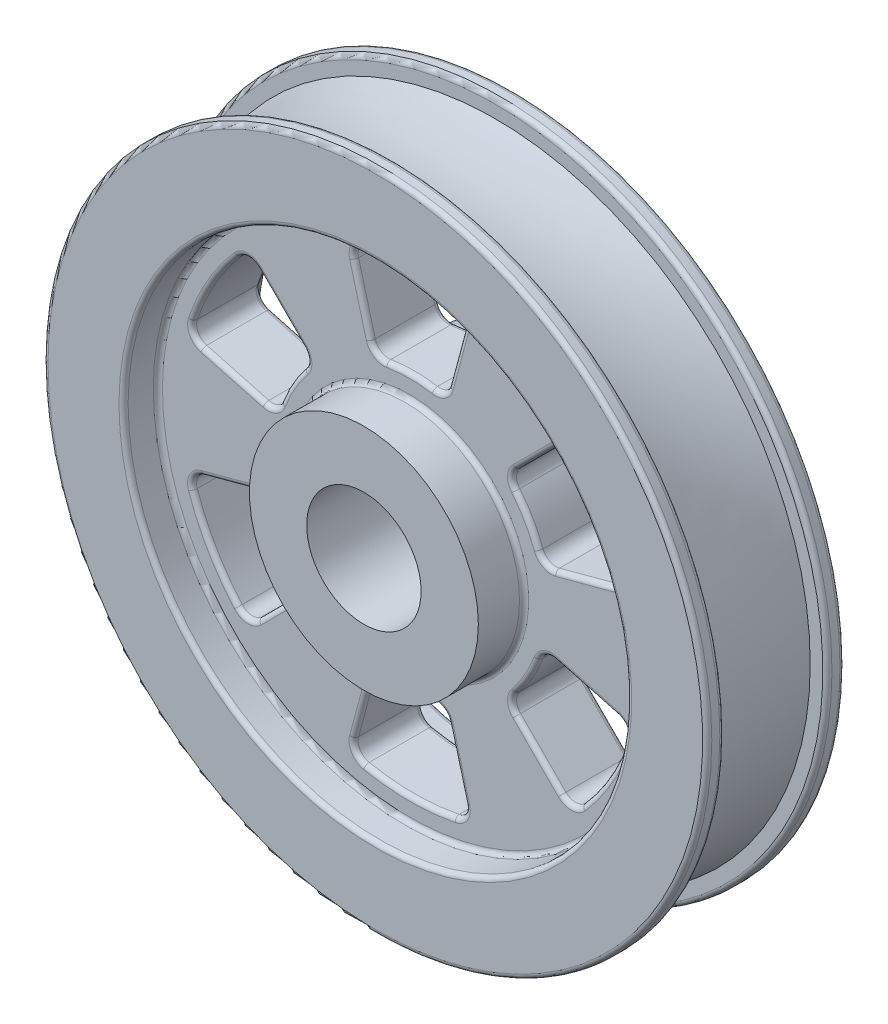
SolidWorks part; units mm, degrees
material "Cast Alloy Steel"
ref_plane "Front Plane" through (0, 0, 0) normal (0, 0, 1) x (1, 0, 0)
ref_plane "Top Plane" through (0, 0, 0) normal (0, 1, 0) x (1, 0, 0)
ref_plane "Right Plane" through (0, 0, 0) normal (1, 0, 0) x (0, 0, -1)
sketch "Wheel Cross-section" plane through (0, 0, 0) normal (1, 0, 0) x (0, 0, -1)
  line L0 (-130.7747, 0) -> (134.6553, 0) construction
  line L1 (44.45, 31.75) -> (44.45, 63.5)
  line L2 (44.45, 63.5) -> (19.05, 63.5)
  line L3 (19.05, 63.5) -> (19.05, 139.7)
  line L4 (19.05, 139.7) -> (38.1, 139.7)
  line L5 (38.1, 139.7) -> (38.1, 184.15)
  line L6 (38.1, 184.15) -> (28.575, 184.15)
  line L7 (28.575, 184.15) -> (28.575, 174.625)
  line L9 (-28.575, 174.625) -> (-28.575, 184.15)
  line L10 (-28.575, 184.15) -> (-38.1, 184.15)
  line L11 (-38.1, 184.15) -> (-38.1, 139.7)
  line L12 (-38.1, 139.7) -> (-19.05, 139.7)
  line L13 (-19.05, 139.7) -> (-19.05, 63.5)
  line L14 (-19.05, 63.5) -> (-44.45, 63.5)
  line L15 (-44.45, 63.5) -> (-44.45, 31.75)
  line L17 (-44.45, 31.75) -> (44.45, 31.75)
  arc A0 (28.575, 174.625) -> (-28.575, 174.625) centre (0, 324.3221) cw
  dimension "D13" = 152.4
  dimension "D14" = 9.525
  dimension "D1" = 44.45
  dimension "D2" = 88.9
  dimension "D3" = 25.4
  dimension "D4" = 38.1
  dimension "D5" = 63.5
  dimension "D6" = 76.2
  dimension "D7" = 9.525
  dimension "D8" = 9.525
  dimension "D9" = 31.75
  dimension "D10" = 6.35
  dimension "D11" = 139.7
  dimension "D12" = 184.15
revolve "Revolve1" add sketch "Wheel Cross-section" angle 360 about L0
sketch "Spoke cut-out" plane through (0, 0, 19.05) normal (0, 0, 1) x (1, 0, 0)
  line L0 (0, 0) -> (-60.1063, 224.3199) construction
  line L1 (0, 0) -> (0, 216.2459) construction
  line L2 (0, 0) -> (59.3665, 221.5588) construction
  line L3 (30.8348, 115.0771) -> (21.6044, 80.6286)
  line L4 (-30.8348, 115.0771) -> (-21.6044, 80.6286)
  circle A0 centre (0, 0) radius 127 construction
  circle A1 centre (0, 0) radius 76.2 construction
  arc A2 (24.9728, 124.5205) -> (-24.9728, 124.5205) centre (0, 0) ccw
  arc A3 (12.9491, 75.0917) -> (-12.9491, 75.0917) centre (0, 0) ccw
  arc A4 (24.9728, 124.5205) -> (30.8348, 115.0771) centre (23.4745, 117.0493) cw
  arc A5 (-24.9728, 124.5205) -> (-30.8348, 115.0771) centre (-23.4745, 117.0493) ccw
  arc A6 (-12.9491, 75.0917) -> (-21.6044, 80.6286) centre (-14.244, 82.6008) cw
  arc A7 (12.9491, 75.0917) -> (21.6044, 80.6286) centre (14.244, 82.6008) ccw
  point P13 (32.87, 122.6726)
  point P16 (-32.87, 122.6726)
  point P19 (-19.722, 73.6035)
  point P22 (19.722, 73.6035)
  dimension "D1" = 254
  dimension "D2" = 152.4
  dimension "D5" = 7.62
  dimension "D6" = 7.62
  dimension "D7" = 7.62
  dimension "D3" = 15
  dimension "D4" = 15
extrude "Spoke hole" cut sketch "Spoke cut-out" against normal through all
pattern_circular "Spoke hole pattern" count 6 over 360 about axis through (0, 0, 0) along (0, 0, 1) of "Spoke hole"
fillet "0.10 inch Fillets & Rounds" radius 2.54 106 edges at (-89.8737, -86.4702, -19.05) (-109.9852, -63.5, -19.05) (-119.8223, -34.5978, -19.05) (-97.8529, -26.2196, -19.05) (-75.1507, -22.1991, -19.05) (-65.9911, -38.1, -19.05) (-56.8003, -53.9828, -19.05) (-18.3504, -76.1819, -19.05) (0, -76.2, -19.05) (18.3504, -76.1819, -19.05) (26.2196, -97.8529, -19.05) (29.9485, -121.0681, -19.05) (0, -127, -19.05) (-29.9485, -121.0681, -19.05) (119.8223, -34.5978, -19.05) (109.9852, -63.5, -19.05) (89.8737, -86.4702, -19.05) (71.6333, -71.6333, -19.05) (56.8003, -53.9828, -19.05) (65.9911, -38.1, -19.05) (75.1507, -22.1991, -19.05) (89.8737, 86.4702, -19.05) (109.9852, 63.5, -19.05) (119.8223, 34.5978, -19.05) (97.8529, 26.2196, -19.05) (75.1507, 22.1991, -19.05) (65.9911, 38.1, -19.05) (56.8003, 53.9828, -19.05) (-29.9485, 121.0681, -19.05) (0, 127, -19.05) (29.9485, 121.0681, -19.05) (26.2196, 97.8529, -19.05) (18.3504, 76.1819, -19.05) (0, 76.2, -19.05) (-18.3504, 76.1819, -19.05) (-119.8223, 34.5978, -19.05) (-109.9852, 63.5, -19.05) (-89.8737, 86.4702, -19.05) (-71.6333, 71.6333, -19.05) (-56.8003, 53.9828, -19.05) (-65.9911, 38.1, -19.05) (-75.1507, 22.1991, -19.05) (18.3504, 76.1819, 19.05) (0, 76.2, 19.05) (-18.3504, 76.1819, 19.05) (-26.2196, 97.8529, 19.05) (-29.9485, 121.0681, 19.05) (0, 127, 19.05) (29.9485, 121.0681, 19.05) (75.1507, 22.1991, 19.05) (65.9911, 38.1, 19.05) (56.8003, 53.9828, 19.05) (71.6333, 71.6333, 19.05) (89.8737, 86.4702, 19.05) (109.9852, 63.5, 19.05) (119.8223, 34.5978, 19.05) (56.8003, -53.9828, 19.05) (65.9911, -38.1, 19.05) (75.1507, -22.1991, 19.05) (97.8529, -26.2196, 19.05) (119.8223, -34.5978, 19.05) (109.9852, -63.5, 19.05) (89.8737, -86.4702, 19.05) (-18.3504, -76.1819, 19.05) (0, -76.2, 19.05) (18.3504, -76.1819, 19.05) (26.2196, -97.8529, 19.05) (29.9485, -121.0681, 19.05) (0, -127, 19.05) (-29.9485, -121.0681, 19.05) (-119.8223, -34.5978, 19.05) (-97.8529, -26.2196, 19.05) (-75.1507, -22.1991, 19.05) (-65.9911, -38.1, 19.05) (-56.8003, -53.9828, 19.05) (-71.6333, -71.6333, 19.05) (-89.8737, -86.4702, 19.05) (-89.8737, 86.4702, 19.05) (-71.6333, 71.6333, 19.05) (-56.8003, 53.9828, 19.05) (-65.9911, 38.1, 19.05) (-75.1507, 22.1991, 19.05) (-97.8529, 26.2196, 19.05) (-119.8223, 34.5978, 19.05) (184.15, 0, -28.575) (184.15, 0, 28.575) (184.15, 0, 38.1) (184.15, 0, -38.1) (139.7, 0, -38.1) (139.7, 0, 38.1) (139.7, 0, -19.05) (-71.6333, -71.6333, -19.05) (-26.2196, -97.8529, -19.05) (97.8529, -26.2196, -19.05) (71.6333, 71.6333, -19.05) (-26.2196, 97.8529, -19.05) (-97.8529, 26.2196, -19.05) (63.5, 0, -19.05) (139.7, 0, 19.05) (63.5, 0, 19.05) (26.2196, 97.8529, 19.05) (97.8529, 26.2196, 19.05) (71.6333, -71.6333, 19.05) (-26.2196, -97.8529, 19.05) (-109.9852, -63.5, 19.05) (-109.9852, 63.5, 19.05)
